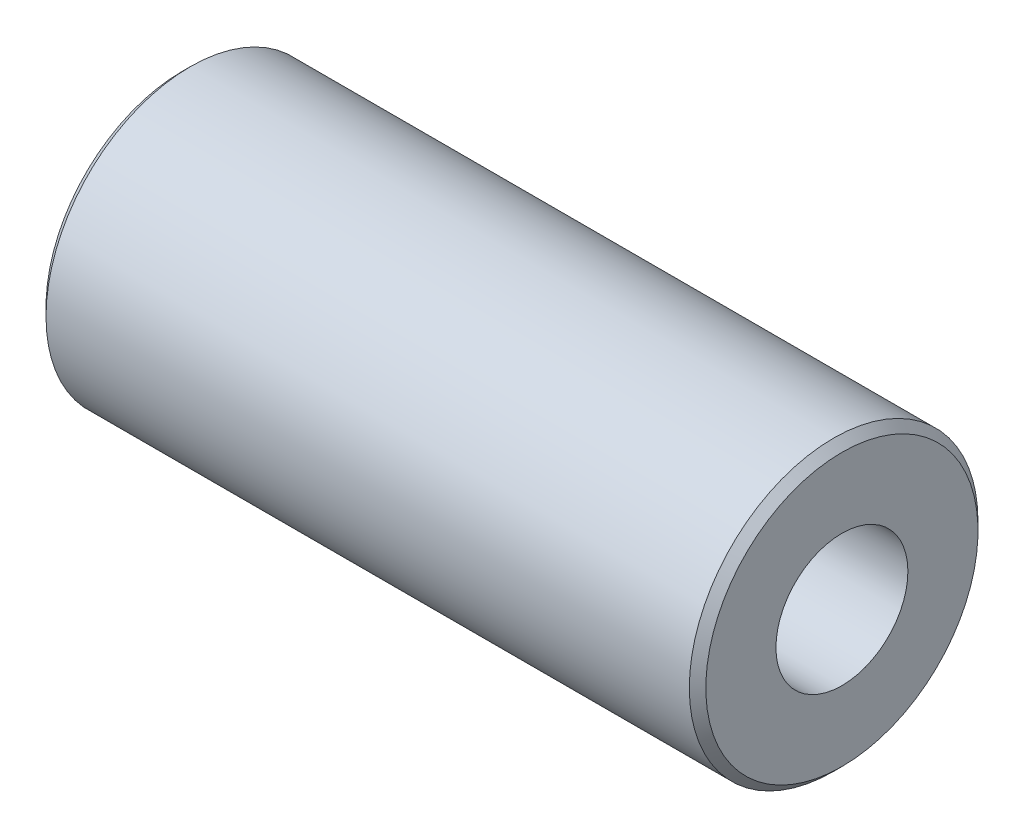
SolidWorks part; units mm, degrees
material "6061 合金"
ref_plane "前视基准面" through (0, 0, 0) normal (0, 0, 1) x (1, 0, 0)
ref_plane "上视基准面" through (0, 0, 0) normal (0, 1, 0) x (1, 0, 0)
ref_plane "右视基准面" through (0, 0, 0) normal (1, 0, 0) x (0, 0, -1)
sketch "草图1" plane through (0, 0, 0) normal (0, 0, 1) x (1, 0, 0)
  line L0 (-4, 0) -> (4, 0) construction
  line L1 (4, 0) -> (4, 1.75)
  line L2 (4, 1.75) -> (-4, 1.75)
  line L3 (-4, 1.75) -> (-4, 0)
  line L4 (4, 0) -> (-4, 0)
  point P4 (0, 0)
  dimension "D1" = 8
  dimension "D2" = 3.5
revolve "旋转1" add sketch "草图1" angle 360 about L0
hole_wizard "螺纹孔" positions "草图2" profile "草图3" tap size "M2" standard "GB"
sketch "草图2" plane through (-4, 0, 0) normal (-1, 0, 0) x (0, 0, 1)
  point P0 (0, 0)
sketch "草图3" plane through (-4, 0, 0) normal (0, 1, 0) x (0, 0, 1)
  line L0 (0, 0) -> (0, 6.4807)
  line L1 (0, 6.4807) -> (0.8, 6)
  line L2 (0.8, 6) -> (0.8, 0)
  line L5 (0.8, 0) -> (0, 0)
  line L10 (0, 6.4807) -> (-0.8, 6) construction
  line L11 (0, -6.35) -> (0, 107.95) construction
  dimension "螺纹孔钻头直径" = 1.6
  dimension "螺纹孔钻头深度" = 6
  dimension "导头角度" = 118
cosmetic thread "孔螺蚊线1" parameters "D1"=6, "D2"=2.9
mirror "镜向1" about plane through (0, 0, 0) normal (1, 0, 0) of "螺纹孔"
cosmetic thread "孔螺蚊线2" parameters "D1"=6, "D2"=2.9
chamfer "倒角1" distance 0.1 angle 45 2 edges at (4, -1.75, 0) (-4, -1.75, 0)
